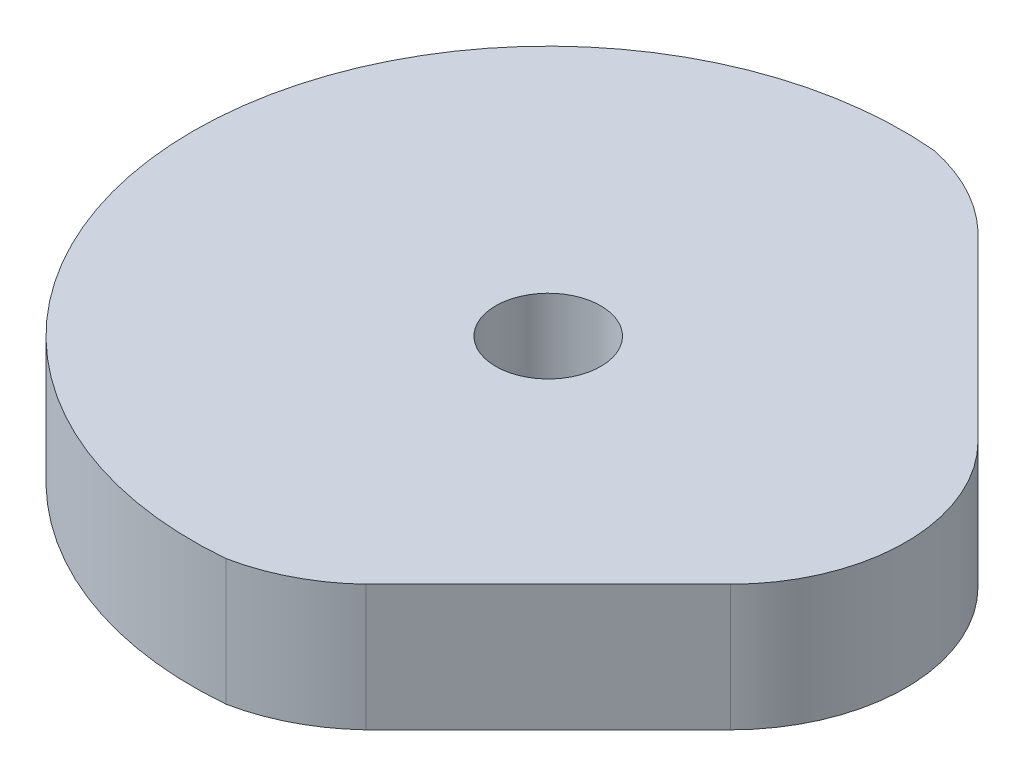
SolidWorks part; units mm, degrees
ref_plane "Front Plane" through (0, 0, 0) normal (0, 0, 1) x (1, 0, 0)
ref_plane "Top Plane" through (0, 0, 0) normal (0, 1, 0) x (1, 0, 0)
ref_plane "Right Plane" through (0, 0, 0) normal (1, 0, 0) x (0, 0, -1)
sketch "Sketch1" plane through (0, 0, 0) normal (0, 1, 0) x (1, 0, 0)
  line L0 (0, 8.5) -> (0, -8.5) construction
  line L1 (8.5, 0) -> (-8.5, 0) construction
  line L2 (0, 0) -> (6.0104, -6.0104) construction
  line L3 (7.2816, -2.9416) -> (2.9416, -7.2816)
  line L4 (7.2816, 2.9416) -> (2.9416, 7.2816)
  line L6 (0, 0) -> (8.5, 0) construction
  arc A0 (7.2816, 2.9416) -> (7.2816, -2.9416) centre (4.34, 0) cw
  arc A1 (0.7526, -8.4147) -> (2.9416, -7.2816) centre (-0.1243, -4.0399) ccw
  circle A2 centre (0, 0) radius 1.25
  arc A4 (0.7526, 8.4147) -> (2.9416, 7.2816) centre (-0.1243, 4.0399) cw
  arc A5 (0.7526, 8.4147) -> (0.7526, -8.4147) centre (0, 0) ccw
  dimension "D1" = 8.5
  dimension "D2" = 17
  dimension "D3" = 17
extrude "Boss-Extrude1" add sketch "Sketch1" along normal blind 3 contours A5 A1 L3 A0 L4 A4 A2
